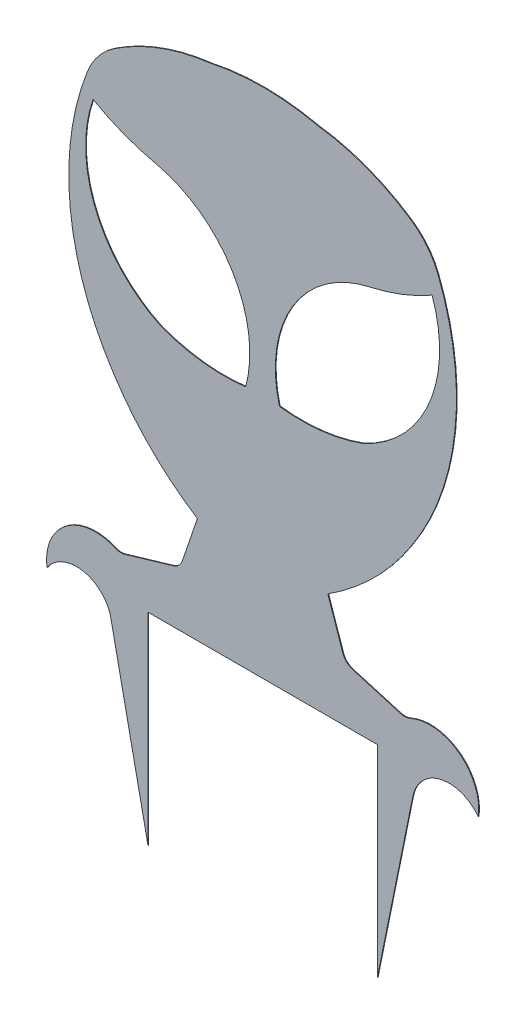
SolidWorks part; units mm, degrees
ref_plane "Alzado" through (0, 0, 0) normal (0, 0, 1) x (1, 0, 0)
ref_plane "Planta" through (0, 0, 0) normal (0, 1, 0) x (1, 0, 0)
ref_plane "Vista lateral" through (0, 0, 0) normal (1, 0, 0) x (0, 0, -1)
sketch "Model" plane through (0, 0, 0) normal (0, 0, 1) x (1, 0, 0)
  line L0 (14.5203, 27.4793) -> (30.0203, 27.4793)
  line L1 (14.5203, -0.7332) -> (14.5203, 27.4793)
  line L2 (46.5203, 27.4793) -> (46.5203, -0.7332)
  line L3 (30.9955, 27.4793) -> (46.5203, 27.4793)
  line L4 (43.041, 34.8302) -> (49.7425, 32.8591)
  line L5 (39.6183, 42.2443) -> (41.6842, 36.193)
  line L6 (19.3505, 36.1914) -> (21.4155, 42.243)
  line L7 (11.2927, 32.8564) -> (17.9938, 34.8284)
  line L8 (51.4711, 23.6593) -> (46.5203, -0.7332)
  line L9 (9.2634, 24.5342) -> (14.5203, -0.7332)
  line L10 (30.0203, 27.4793) -> (30.9955, 27.4793)
  arc A0 (60.6176, 25.8068) -> (51.1153, 32.9486) centre (53.8685, 26.7194) ccw
  arc A1 (49.7425, 32.8591) -> (51.1153, 32.9486) centre (50.3068, 34.7779) ccw
  arc A2 (41.6842, 36.193) -> (43.041, 34.8302) centre (43.6054, 36.7489) ccw
  arc A3 (39.6183, 42.2443) -> (51.2913, 53.8891) centre (18.8873, 74.6985) ccw
  arc A4 (51.2913, 53.8891) -> (54.992, 88.5416) centre (19.6205, 74.7952) ccw
  arc A5 (54.992, 88.5416) -> (51.2221, 93.2371) centre (45.6711, 84.9192) ccw
  arc A6 (51.2221, 93.2371) -> (38.2445, 98.1256) centre (34.5172, 68.5607) ccw
  arc A7 (38.2445, 98.1256) -> (23.1836, 98.1753) centre (30.6022, 64.2404) ccw
  arc A8 (23.1836, 98.1753) -> (9.8043, 93.2341) centre (26.8201, 67.7447) ccw
  arc A9 (9.8043, 93.2341) -> (6.0351, 88.538) centre (15.3565, 84.917) ccw
  arc A10 (6.0351, 88.538) -> (9.7409, 53.886) centre (41.4086, 74.7968) ccw
  arc A11 (9.7409, 53.886) -> (21.4155, 42.243) centre (42.1418, 74.7002) ccw
  arc A12 (17.9938, 34.8284) -> (19.3505, 36.1914) centre (17.4292, 36.747) ccw
  arc A13 (9.9198, 32.9456) -> (11.2927, 32.8564) centre (10.7281, 34.775) ccw
  arc A14 (9.9198, 32.9456) -> (0.4186, 25.8025) centre (7.1675, 26.716) ccw
  arc A15 (60.6176, 25.8068) -> (51.4711, 23.6593) centre (56.5289, 22.6693) ccw
  arc A16 (9.2634, 24.5342) -> (0.4186, 25.8025) centre (4.5384, 23.0584) ccw
  arc A17 (28.1532, 61.5258) -> (15.5428, 82.2552) centre (11.9586, 65.8744) ccw
  arc A18 (6.86, 85.6136) -> (15.5428, 82.2552) centre (22.1253, 112.1765) ccw
  arc A19 (6.86, 85.6136) -> (16.4426, 62.8944) centre (24.1242, 79.515) ccw
  arc A20 (16.4426, 62.8944) -> (28.1532, 61.5258) centre (25.1067, 86.243) ccw
  arc A21 (32.8667, 61.5232) -> (44.5882, 62.8965) centre (35.9119, 86.2405) ccw
  arc A22 (44.5882, 62.8965) -> (54.1675, 85.6171) centre (36.9042, 79.5159) ccw
  arc A23 (45.4852, 82.2573) -> (54.1675, 85.6171) centre (38.8983, 112.1777) ccw
  arc A24 (45.4852, 82.2573) -> (32.8667, 61.5232) centre (49.0605, 65.8747) ccw
extrude "Saliente-Extruir1" add sketch "Model" along normal blind 0.1
